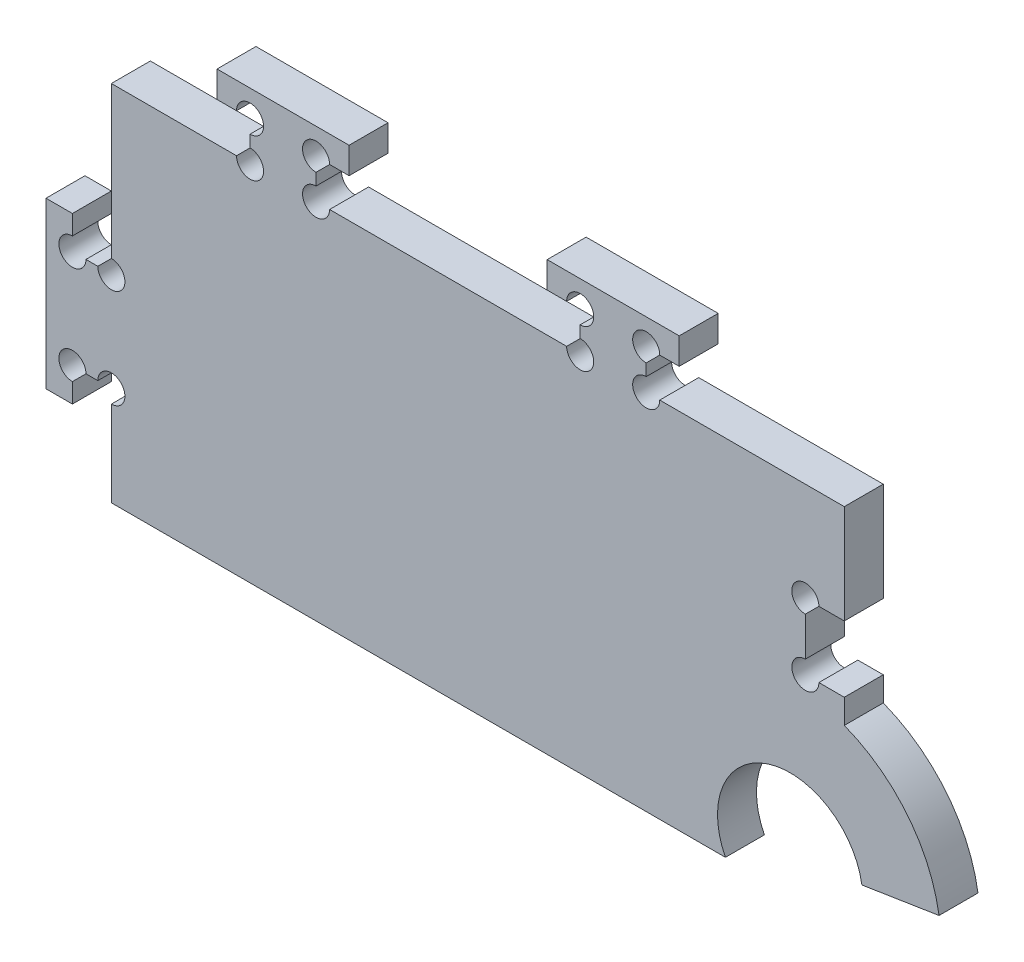
SolidWorks part; units mm, degrees
ref_plane "Front Plane" through (0, 0, 0) normal (0, 0, 1) x (1, 0, 0)
ref_plane "Top Plane" through (0, 0, 0) normal (0, 1, 0) x (1, 0, 0)
ref_plane "Right Plane" through (0, 0, 0) normal (1, 0, 0) x (0, 0, -1)
sketch "Sketch1" plane through (0, 0, 0) normal (0, 0, 1) x (1, 0, 0)
  line L0 (-17.6033, 83.9872) -> (76.3967, 83.9872) construction
  line L1 (86.1956, 88.9853) -> (94.3967, 110.2893) construction
  line L2 (86.1956, 88.9853) -> (108.746, 92.535) construction
  line L3 (76.3967, 83.9872) -> (-17.6033, 83.9872)
  line L4 (-17.6033, 83.9872) -> (-17.6033, 138.9872)
  line L5 (-17.6033, 138.9872) -> (94.3967, 138.9872)
  line L6 (94.3967, 138.9872) -> (94.3967, 110.2893)
  line L7 (108.746, 92.535) -> (97.0618, 90.6958)
  arc A0 (108.746, 92.535) -> (94.3967, 110.2893) centre (86.1956, 88.9853) ccw
  arc A1 (97.0618, 90.6958) -> (76.3967, 83.9872) centre (86.1956, 88.9853) ccw
  arc A2 (72.0509, 71.0676) -> (86.3967, 66.1582) centre (86.1956, 88.9853) ccw construction
  dimension "D1" = 60
  dimension "D2" = 112
  dimension "D3" = 55
  dimension "D4" = 90
extrude "Boss-Extrude1" add sketch "Sketch1" along normal blind 5.9 contours A1 L7 A0 L6 L5 L4 L3
sketch "Sketch2" plane through (0, 0, 5.9) normal (0, 0, 1) x (1, 0, 0)
  line L0 (76.3967, 83.9872) -> (-17.6033, 83.9872) construction
  line L1 (-17.6033, 138.9872) -> (-25.6033, 138.9872)
  line L2 (-17.6033, 138.9872) -> (-17.6033, 83.9872)
  line L3 (-17.6033, 83.9872) -> (-25.6033, 83.9872)
  line L4 (-25.6033, 138.9872) -> (-25.6033, 83.9872)
  dimension "D1" = 8
extrude "Boss-Extrude2" add sketch "Sketch2" against normal blind 8
sketch "Sketch3" plane through (0, 0, 5.9) normal (0, 0, 1) x (1, 0, 0)
  line L5 (-25.6033, 138.9872) -> (-25.6033, 83.9872) construction
  line L7 (94.3967, 123.9872) -> (88.4967, 123.9872)
  line L8 (94.3967, 123.9872) -> (94.3967, 113.9872)
  line L9 (94.3967, 113.9872) -> (88.4967, 113.9872)
  line L10 (88.4967, 123.9872) -> (88.4967, 113.9872)
  line L11 (94.3967, 138.9872) -> (94.3967, 110.2893) construction
  line L12 (76.3967, 83.9872) -> (-25.6033, 83.9872) construction
  line L13 (-25.6033, 98.9872) -> (-16.6033, 98.9872)
  line L14 (-25.6033, 98.9872) -> (-25.6033, 83.9872)
  line L15 (-25.6033, 83.9872) -> (-16.6033, 83.9872)
  line L16 (-16.6033, 98.9872) -> (-16.6033, 83.9872)
  line L18 (-25.6033, 138.9872) -> (94.3967, 138.9872) construction
  dimension "D3" = 10
  dimension "D4" = 5.9
  dimension "D5" = 0
  dimension "D6" = 9
  dimension "D7" = 15
  dimension "D8" = 15
extrude "Cut-Extrude1" cut sketch "Sketch3" against normal through all
sketch "Sketch4" plane through (0, 0, 5.9) normal (0, 0, 1) x (1, 0, 0)
  line L0 (4.3967, 138.9872) -> (4.3967, 144.8872)
  line L1 (-25.6033, 138.9872) -> (94.3967, 138.9872) construction
  line L2 (4.3967, 144.8872) -> (-0.6033, 144.8872)
  line L3 (-0.6033, 144.8872) -> (-0.6033, 148.8872)
  line L4 (-0.6033, 148.8872) -> (19.3967, 148.8872)
  line L5 (19.3967, 148.8872) -> (19.3967, 144.8872)
  line L6 (19.3967, 144.8872) -> (14.3967, 144.8872)
  line L7 (14.3967, 144.8872) -> (14.3967, 138.9872)
  line L8 (14.3967, 138.9872) -> (4.3967, 138.9872)
  line L9 (49.3967, 144.8872) -> (49.3967, 148.8872)
  line L10 (69.3967, 148.8872) -> (69.3967, 144.8872)
  line L11 (49.3967, 148.8872) -> (69.3967, 148.8872)
  line L12 (54.3967, 144.8872) -> (49.3967, 144.8872)
  line L13 (69.3967, 144.8872) -> (64.3967, 144.8872)
  line L14 (64.3967, 144.8872) -> (64.3967, 138.9872)
  line L15 (64.3967, 138.9872) -> (54.3967, 138.9872)
  line L16 (54.3967, 138.9872) -> (54.3967, 144.8872)
  line L17 (-25.6033, 138.9872) -> (-25.6033, 98.9872) construction
  point P4 (9.3967, 148.8872)
  point P11 (9.3967, 138.9872)
  dimension "D1" = 5.9
  dimension "D2" = 10
  dimension "D3" = 20
  dimension "D4" = 4
  dimension "D6" = 30
  dimension "D5" = 2
extrude "Boss-Extrude3" add sketch "Sketch4" against normal up to surface (5.9 mm away) up to face at (58.9862, 109.8016, 0)
sketch "Sketch5" plane through (0, 0, 5.9) normal (0, 0, 1) x (1, 0, 0)
  line L0 (-25.6033, 123.9872) -> (-33.6033, 123.9872)
  line L2 (-25.6033, 138.9872) -> (-25.6033, 98.9872) construction
  line L3 (-33.6033, 123.9872) -> (-33.6033, 128.9872)
  line L4 (-33.6033, 128.9872) -> (-37.6033, 128.9872)
  line L5 (-37.6033, 128.9872) -> (-37.6033, 103.9872)
  line L6 (-37.6033, 103.9872) -> (-33.6033, 103.9872)
  line L7 (-33.6033, 103.9872) -> (-33.6033, 108.9872)
  line L8 (-33.6033, 108.9872) -> (-25.6033, 108.9872)
  line L9 (-25.6033, 108.9872) -> (-25.6033, 123.9872)
  line L10 (-25.6033, 138.9872) -> (4.3967, 138.9872) construction
  point P12 (-37.6033, 116.4872)
  point P13 (-25.6033, 116.4872)
  dimension "D1" = 8
  dimension "D2" = 15
  dimension "D3" = 25
  dimension "D4" = 4
  dimension "D5" = 15
extrude "Boss-Extrude4" add sketch "Sketch5" against normal through all
sketch "Sketch6" plane through (0, 0, 5.9) normal (0, 0, 1) x (1, 0, 0)
  line L1 (-16.6033, 83.9872) -> (-44.1864, 83.9872)
  line L2 (-16.6033, 83.9872) -> (-16.6033, 152.4435)
  line L3 (-16.6033, 152.4435) -> (-44.1864, 152.4435)
  line L4 (-44.1864, 83.9872) -> (-44.1864, 152.4435)
extrude "Cut-Extrude2" cut sketch "Sketch6" against normal through all
sketch "Sketch7" plane through (0, 0, 5.9) normal (0, 0, 1) x (1, 0, 0)
  line L0 (-16.6033, 113.9872) -> (-22.5033, 113.9872)
  line L1 (-16.6033, 83.9872) -> (-16.6033, 138.9872) construction
  line L2 (-22.5033, 113.9872) -> (-22.5033, 118.9872)
  line L3 (-22.5033, 118.9872) -> (-26.5033, 118.9872)
  line L4 (-26.5033, 118.9872) -> (-26.5033, 93.9872)
  line L5 (-26.5033, 93.9872) -> (-22.5033, 93.9872)
  line L6 (-22.5033, 93.9872) -> (-22.5033, 98.9872)
  line L7 (-22.5033, 98.9872) -> (-16.6033, 98.9872)
  line L8 (-16.6033, 98.9872) -> (-16.6033, 113.9872)
  line L9 (-16.6033, 138.9872) -> (4.3967, 138.9872) construction
  point P4 (-26.5033, 106.4872)
  point P11 (-16.6033, 106.4872)
  dimension "D4" = 5.9
  dimension "D1" = 15
  dimension "D2" = 25
  dimension "D3" = 4
  dimension "D5" = 25
extrude "Boss-Extrude5" add sketch "Sketch7" against normal up to surface (5.9 mm away) up to face at (50.0879, 131.1126, 0)
sketch "Sketch8" plane through (0, 0, 5.9) normal (0, 0, 1) x (1, 0, 0)
  circle A0 centre (-16.6033, 98.9872) radius 2.05
  circle A1 centre (-22.5033, 98.9872) radius 2.05
  circle A2 centre (-22.5033, 113.9872) radius 2.05
  circle A3 centre (-16.6033, 113.9872) radius 2.05
  circle A4 centre (4.3967, 138.9872) radius 2.05
  circle A5 centre (14.3967, 138.9872) radius 2.05
  circle A6 centre (14.3967, 144.8872) radius 2.05
  circle A7 centre (4.3967, 144.8872) radius 2.05
  circle A8 centre (54.3967, 144.8872) radius 2.05
  circle A9 centre (54.3967, 138.9872) radius 2.05
  circle A10 centre (64.3967, 138.9872) radius 2.05
  circle A11 centre (64.3967, 144.8872) radius 2.05
  circle A12 centre (88.4967, 123.9872) radius 2.05
  circle A13 centre (88.4967, 113.9872) radius 2.05
  dimension "D1" = 4.1
extrude "Cut-Extrude3" cut sketch "Sketch8" against normal up to next
equation "\"e\" = 5.9"
equation "\"D1@Boss-Extrude1\"= \"e\""
equation "\"D4@Sketch3\"= \"e\""
equation "\"D1@Sketch4\"= \"e\""
equation "\"D4@Sketch7\"= \"e\""
